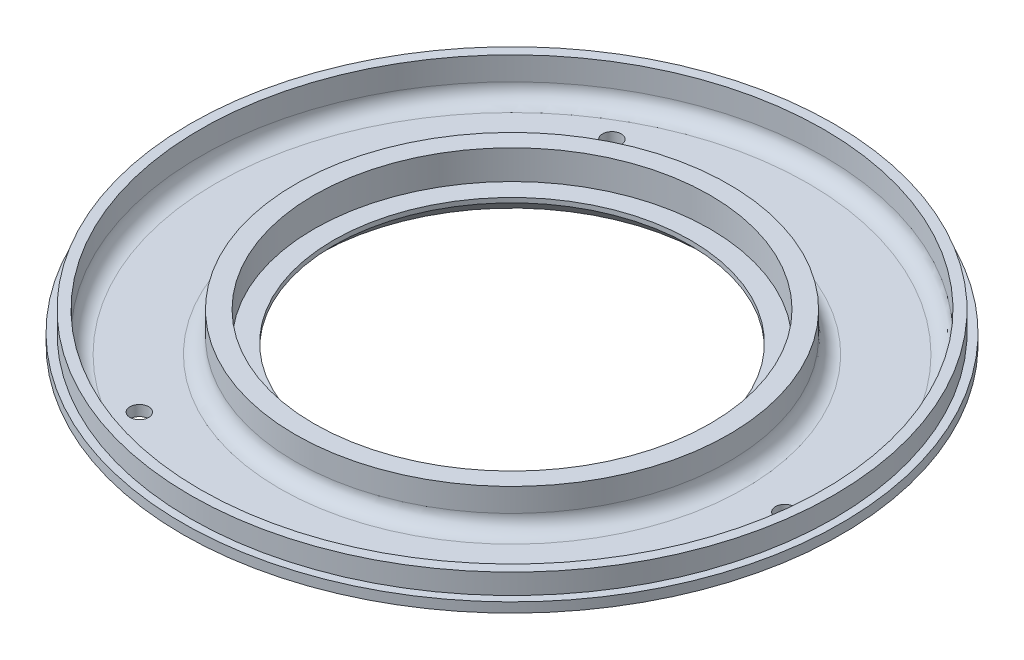
SolidWorks part; units mm, degrees
material "6061-T6 (SS)"
ref_plane "Front Plane" through (0, 0, 0) normal (0, 0, 1) x (1, 0, 0)
ref_plane "Top Plane" through (0, 0, 0) normal (0, 1, 0) x (1, 0, 0)
ref_plane "Right Plane" through (0, 0, 0) normal (1, 0, 0) x (0, 0, -1)
sketch "Sketch2" plane through (0, 0, 0) normal (1, 0, 0) x (0, 0, -1)
  line L0 (-45.8, 0) -> (-82.55, 0)
  line L1 (-82.55, 0) -> (-82.55, 12.7)
  line L2 (-82.55, 12.7) -> (-50.8, 12.7)
  line L3 (-45.8, 0) -> (-45.8, 5.2)
  line L4 (-45.8, 5.2) -> (-50.8, 5.2)
  line L5 (-50.8, 5.2) -> (-50.8, 12.7)
  line L6 (-80.2166, 12.7) -> (-80.2166, 0) construction
  dimension "D1" = 82.55
  dimension "D2" = 12.7
  dimension "D3" = 50.8
  dimension "D4" = 5
  dimension "D5" = 7.5
ref_axis "Axis1" through (0, -0.635, 0) along (0, 1, 0)
revolve "Revolve1" add sketch "Sketch2" angle 360 about axis through (0, -0.635, 0) along (0, 1, 0)
hole_wizard "#90 (0.0087) Diameter Hole1" positions "Sketch6" profile "Sketch7" hole size "#90" standard "ANSI Inch" end condition through all
sketch "Sketch6" plane through (0, 12.7, 0) normal (0, 1, 0) x (1, 0, 0)
  line L0 (0, 0) -> (-69.8201, 120.932) construction
  line L2 (0, 0) -> (0, 109.0908) construction
  point P0 (-35, 60.6218)
  dimension "D1" = 30
  dimension "D2" = 70
sketch "Sketch7" plane through (-35, 12.7, -60.6218) normal (1, 0, 0) x (0, 0, 1)
  line L0 (0, 0) -> (0, 12.7)
  line L1 (0, 12.7) -> (0.1105, 12.7)
  line L2 (0.1105, 12.7) -> (0.1105, 0)
  line L5 (0.1105, 0) -> (0, 0)
  line L11 (0, -6.35) -> (0, 107.95) construction
  dimension "Thru Hole Dia." = 0.221
  dimension "Thru Hole Depth" = 12.7
pattern_circular "CirPattern3" count 3 over 360 about axis through (0, 0, 0) along (0, 1, 0) of "#90 (0.0087) Diameter Hole1"
sketch "Sketch8" plane through (0, 12.7, 0) normal (0, 1, 0) x (1, 0, 0)
  circle A0 centre (0, 0) radius 55.626
  circle A1 centre (0, 0) radius 80.01
  circle A2 centre (0, 0) radius 82.55 construction
  dimension "D1" = 26.924
  dimension "D2" = 2.54
extrude "Cut-Extrude1" cut sketch "Sketch8" against normal blind 10
fillet "Fillet5" radius 4 2 edges at (0, 2.7, 55.626) (0, 2.7, 80.01)
chamfer "Chamfer1" distance 4 angle 45 1 edges at (0, 0, -45.8)
sketch "Sketch10" plane through (0, 0, 0) normal (0, -1, 0) x (1, 0, 0)
  circle A0 centre (0, 0) radius 82.55
  circle A1 centre (0, 0) radius 84.55
  circle A2 centre (0, 0) radius 82.55 construction
  dimension "D1" = 2
extrude "Boss-Extrude1" add sketch "Sketch10" against normal blind 7.5
chamfer "Chamfer3" distance 5 angle 60 1 edges at (0, 0, -84.55)
fillet "Fillet4" radius 5 1 edges at (0, 0, 75.8897)
hole_wizard "#12 (0.189) Diameter Hole1" positions "Sketch13" profile "Sketch14" hole size "#12" standard "ANSI Inch" end condition through all
sketch "Sketch13" plane through (0, 0, 0) normal (0, -1, 0) x (-1, 0, 0)
  point P4 (35, 60.6218)
sketch "Sketch14" plane through (-35, 0, -60.6218) normal (1, 0, 0) x (0, 0, -1)
  line L0 (0, 0) -> (0, 12.7)
  line L1 (0, 12.7) -> (2.4003, 12.7)
  line L2 (2.4003, 12.7) -> (2.4003, 0)
  line L5 (2.4003, 0) -> (0, 0)
  line L11 (0, -6.35) -> (0, 107.95) construction
  dimension "Thru Hole Dia." = 4.8006
  dimension "Thru Hole Depth" = 12.7
pattern_circular "CirPattern5" count 3 over 360 about axis through (0, 0, 0) along (0, 1, 0) of "#12 (0.189) Diameter Hole1"
equation "\"TubeDiameter\" = 6.500in"
